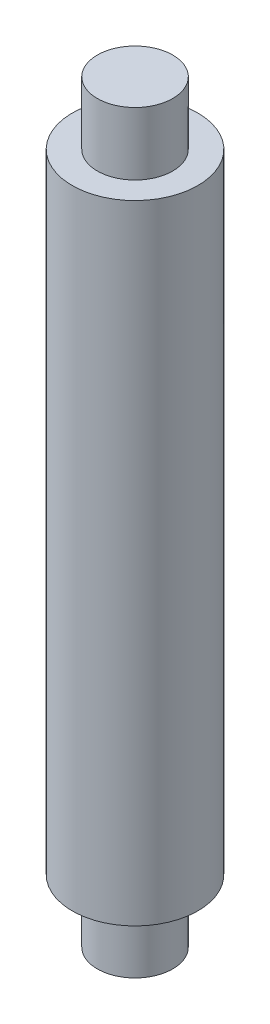
SolidWorks part; units mm, degrees
material "ABS"
ref_plane "Alzado" through (0, 0, 0) normal (0, 0, 1) x (1, 0, 0)
ref_plane "Planta" through (0, 0, 0) normal (0, 1, 0) x (1, 0, 0)
ref_plane "Vista lateral" through (0, 0, 0) normal (1, 0, 0) x (0, 0, -1)
sketch "Croquis1" plane through (0, 0, 0) normal (0, 0, 1) x (1, 0, 0)
  line L0 (0, 0) -> (0, 76.875) construction
  line L1 (0, 60) -> (-6, 60)
  line L2 (-6, 60) -> (-6, 50)
  line L3 (-6, 50) -> (-10, 50)
  line L4 (-10, 50) -> (-10, -50)
  line L5 (-10, -50) -> (-6, -50)
  line L6 (-6, -50) -> (-6, -60)
  line L7 (-6, -60) -> (0, -60)
  line L8 (0, -60) -> (0, 60)
  point P13 (0, 0)
  dimension "D1" = 120
  dimension "D2" = 12
  dimension "D3" = 10
  dimension "D4" = 20
revolve "Revolución1" add sketch "Croquis1" angle 360 about L0
